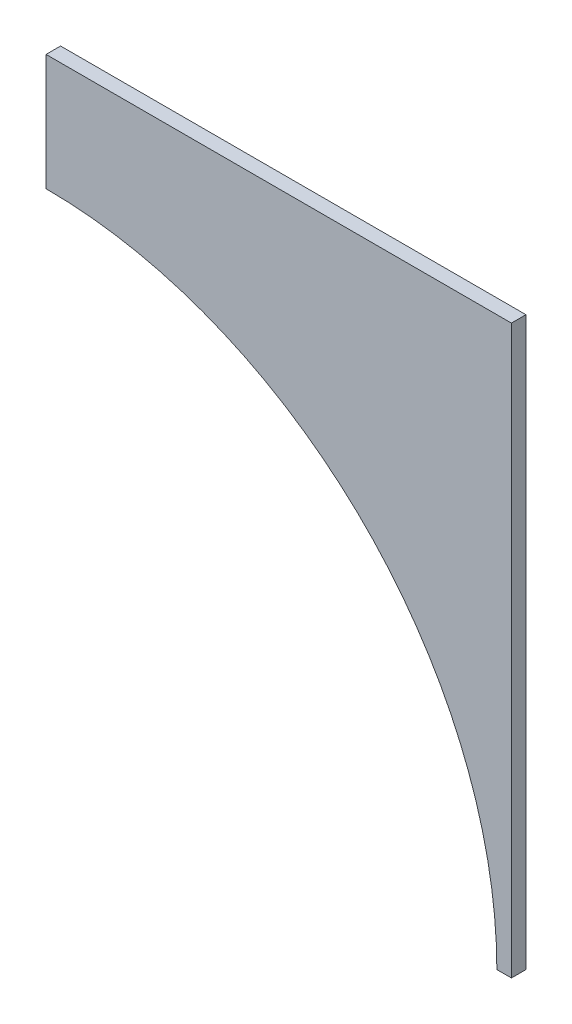
SolidWorks part; units mm, degrees
ref_plane "Front Plane" through (0, 0, 0) normal (0, 0, 1) x (1, 0, 0)
ref_plane "Top Plane" through (0, 0, 0) normal (0, 1, 0) x (1, 0, 0)
ref_plane "Right Plane" through (0, 0, 0) normal (1, 0, 0) x (0, 0, -1)
sketch "Sketch1" plane through (0, 0, 0) normal (0, 0, 1) x (1, 0, 0)
  line L0 (-71.9538, 91.04) -> (29.6462, 91.04)
  line L2 (29.6462, 91.04) -> (29.6462, -32.785)
  line L3 (29.6462, -32.785) -> (26.4712, -32.785)
  line L4 (-71.9538, 91.04) -> (-71.9538, 65.64)
  line L5 (-71.9538, -32.785) -> (26.4712, -32.785) construction
  line L6 (-71.9538, -32.785) -> (-71.9538, 65.64) construction
  line L9 (29.6462, -188.36) -> (29.6462, 91.04) construction
  line L10 (-68.7788, 65.64) -> (-71.9538, 65.64) construction
  line L11 (80.4462, 91.04) -> (29.6462, 91.04) construction
  arc A0 (26.4712, -32.785) -> (-71.9538, 65.64) centre (-71.9538, -32.785) ccw
  point P2 (29.6462, -128.5189)
  point P8 (-71.9538, 4.6676)
  point P10 (-71.9538, -8.3935)
  point P14 (0, 0)
  point P15 (0, 0)
  dimension "D1" = 3.175
extrude "Boss-Extrude1" add sketch "Sketch1" against normal blind 3.175
